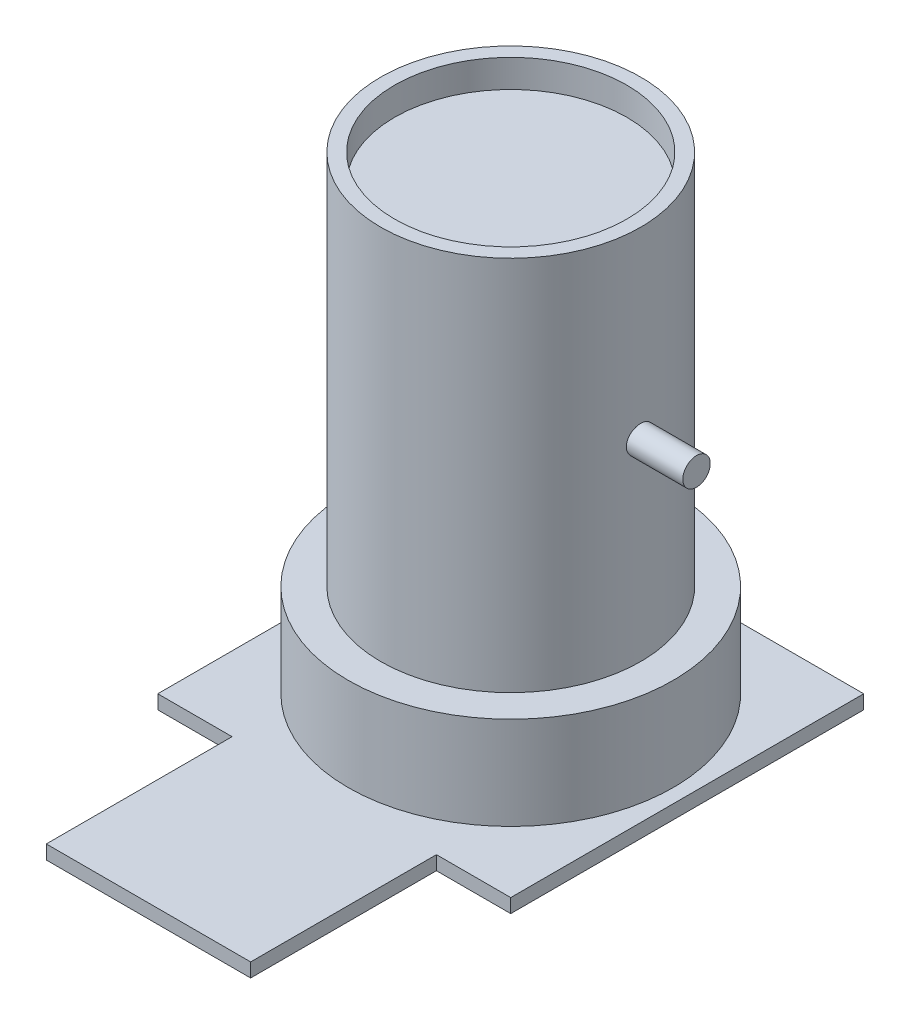
SolidWorks part; units mm, degrees
ref_plane "Front Plane" through (0, 0, 0) normal (0, 0, 1) x (1, 0, 0)
ref_plane "Top Plane" through (0, 0, 0) normal (0, 1, 0) x (1, 0, 0)
ref_plane "Right Plane" through (0, 0, 0) normal (1, 0, 0) x (0, 0, -1)
sketch "Sketch1" plane through (0, 0, 0) normal (0, 1, 0) x (1, 0, 0)
  line L1 (-19, 19) -> (19, 19)
  line L2 (-19, 19) -> (-19, -19)
  line L3 (-19, -19) -> (19, -19)
  line L4 (19, 19) -> (19, -19)
  point P4 (0, 19)
  point P6 (19, 0)
  dimension "D1" = 38
  dimension "D2" = 38
extrude "Boss-Extrude1" add sketch "Sketch1" along normal blind 1.5
sketch "Sketch2" plane through (0, 1.5, 0) normal (0, 1, 0) x (1, 0, 0)
  circle A0 centre (0, 0) radius 17.5
extrude "Boss-Extrude2" add sketch "Sketch2" along normal blind 10
sketch "Sketch3" plane through (0, 11.5, 0) normal (0, 1, 0) x (1, 0, 0)
  circle A0 centre (0, 0) radius 14
extrude "Boss-Extrude3" add sketch "Sketch3" along normal blind 40.5
sketch "Sketch4" plane through (0, 52, 0) normal (0, 1, 0) x (1, 0, 0)
  circle A0 centre (0, 0) radius 12.5
extrude "Cut-Extrude1" cut sketch "Sketch4" against normal blind 3
sketch "Sketch5" plane through (0, 0, 0) normal (1, 0, 0) x (0, 0, -1)
  line L0 (12.5, 52) -> (-12.5, 52) construction
  circle A0 centre (0, 32.23) radius 1.4786
  point P4 (0, 0)
  dimension "D1" = 19.77
extrude "Boss-Extrude4" add sketch "Sketch5" along normal blind 20
sketch "Sketch6" plane through (0, 0, 19) normal (0, 0, 1) x (1, 0, 0)
  line L0 (-11, 1.5) -> (-11, 0)
  line L1 (-19, 1.5) -> (19, 1.5) construction
  line L2 (-19, 0) -> (19, 0) construction
  line L3 (-11, 0) -> (11, 0)
  line L4 (11, 0) -> (11, 1.5)
  line L5 (11, 1.5) -> (-11, 1.5)
  line L7 (-19, 1.5) -> (-19, 0) construction
  point P7 (0, 1.5)
  dimension "D1" = 22
  dimension "D2" = 19
extrude "Boss-Extrude5" add sketch "Sketch6" along normal blind 20
